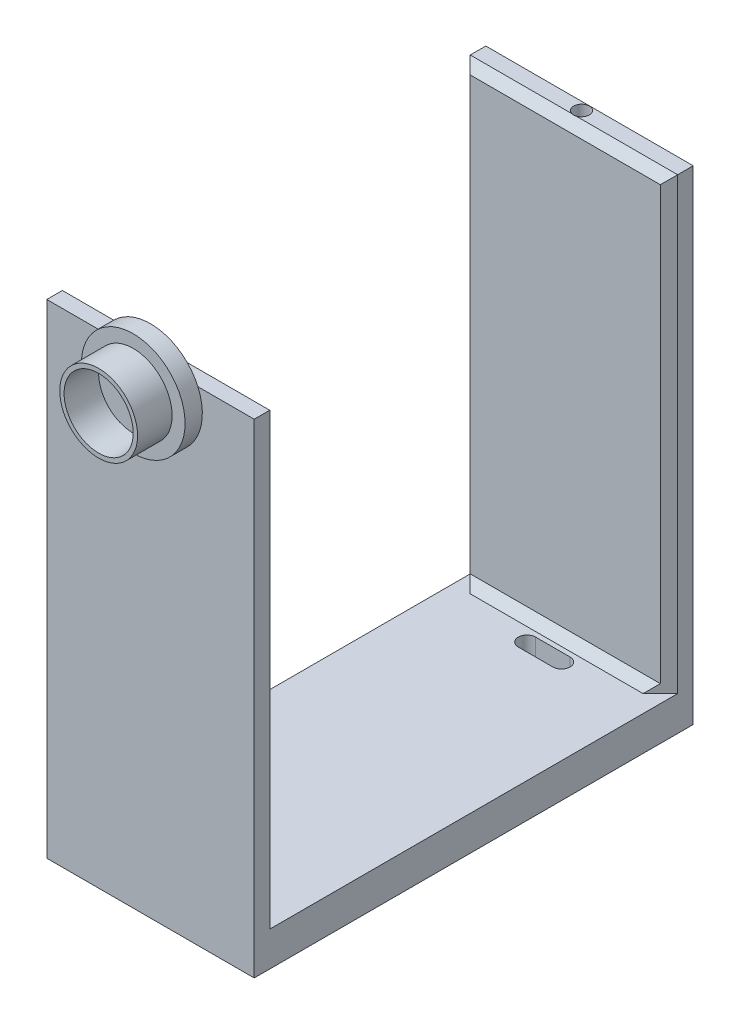
SolidWorks part; units mm, degrees
ref_plane "Front Plane" through (0, 0, 0) normal (0, 0, 1) x (1, 0, 0)
ref_plane "Top Plane" through (0, 0, 0) normal (0, 1, 0) x (1, 0, 0)
ref_plane "Right Plane" through (0, 0, 0) normal (1, 0, 0) x (0, 0, -1)
sketch "Sketch1" plane through (0, 0, 0) normal (0, 1, 0) x (1, 0, 0)
  line L0 (-6, 0) -> (6, 0)
  line L2 (-6, 0) -> (-6, -12.7)
  line L3 (-6, -12.7) -> (6, -12.7)
  line L4 (6, 0) -> (6, -12.7)
  line L5 (0, -12.7) -> (0, 0) construction
  line L6 (-6, 0) -> (6, 0) construction
  point P0 (0, 0)
  dimension "D1" = 12.7
  dimension "D2" = 12
extrude "Boss-Extrude1" add sketch "Sketch1" against normal blind 2
sketch "Sketch2" plane through (0, 0, 0) normal (0, 1, 0) x (1, 0, 0)
  line L0 (6, -12.7) -> (6, 0) construction
  line L1 (-6, -12.7) -> (6, -12.7)
  line L2 (-6, -12.7) -> (-6, -11.3)
  line L3 (-6, -11.3) -> (6, -11.3)
  line L4 (6, -12.7) -> (6, -11.3)
  dimension "D1" = 1.4
extrude "Boss-Extrude2" add sketch "Sketch2" along normal blind 26
mirror "Mirror1" about plane through (0, 0, 0) normal (0, 0, 1) of "Boss-Extrude2", "Boss-Extrude1"
chamfer "Chamfer1" distance 0.5 angle 45 6 edges at (6, 13, -11.3) (-6, 13, -11.3) (0, 26, -11.3) (6, 13, 11.3) (0, 26, 11.3) (-6, 13, 11.3)
chamfer "Chamfer2" distance 0.5 angle 45 2 edges at (0, 0, 11.3) (0, 0, -11.3)
sketch "Sketch3" plane through (0, 26, 0) normal (0, 1, 0) x (1, 0, 0)
  circle A0 centre (0, -12.2374) radius 0.45
  circle A1 centre (0, 12.2374) radius 0.45
  dimension "D1" = 0.9
extrude "Cut-Extrude1" cut sketch "Sketch3" against normal blind 5
sketch "Sketch4" plane through (0, 0, 0) normal (0, 1, 0) x (1, 0, 0)
  line L0 (-0.9449, 10.0239) -> (1.0561, 10.0239) construction
  line L1 (-0.9449, 10.5239) -> (1.0561, 10.5239)
  line L2 (-0.9449, 9.5239) -> (1.0561, 9.5239)
  line L6 (-0.9449, -10.0239) -> (1.0561, -10.0239) construction
  line L7 (-0.9449, -10.5239) -> (1.0561, -10.5239)
  line L8 (-0.9449, -9.5239) -> (1.0561, -9.5239)
  arc A0 (-0.9449, 10.5239) -> (-0.9449, 9.5239) centre (-0.9449, 10.0239) ccw
  arc A1 (1.0561, 9.5239) -> (1.0561, 10.5239) centre (1.0561, 10.0239) ccw
  arc A2 (-0.9449, -10.5239) -> (-0.9449, -9.5239) centre (-0.9449, -10.0239) cw
  arc A3 (1.0561, -9.5239) -> (1.0561, -10.5239) centre (1.0561, -10.0239) cw
  point P2 (0.0556, 10.0239)
  point P15 (0.0556, -10.0239)
  dimension "D1" = 0.5
extrude "Cut-Extrude2" cut sketch "Sketch4" against normal blind 5
sketch "Sketch5" plane through (0, 0, 12.7) normal (0, 0, 1) x (1, 0, 0)
  circle A0 centre (0, 24.7858) radius 3
  dimension "D1" = 6
extrude "Boss-Extrude3" add sketch "Sketch5" along normal blind 1
sketch "Sketch6" plane through (0, 0, 13.7) normal (0, 0, 1) x (1, 0, 0)
  circle A0 centre (0, 24.7994) radius 2.25
  dimension "D1" = 4.5
extrude "Boss-Extrude4" add sketch "Sketch6" along normal blind 2
sketch "Sketch7" plane through (0, 0, 15.7) normal (0, 0, 1) x (1, 0, 0)
  circle A0 centre (0, 24.7994) radius 2
  dimension "D1" = 4
extrude "Cut-Extrude3" cut sketch "Sketch7" against normal blind 2
